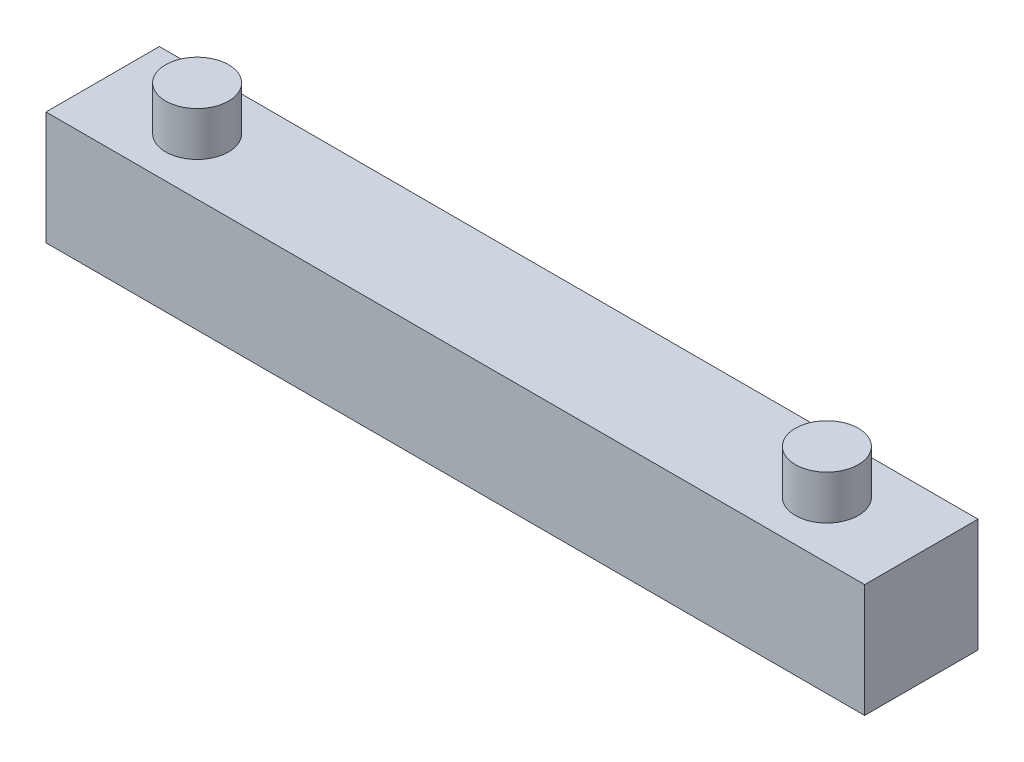
SolidWorks part; units mm, degrees
ref_plane "Front" through (0, 0, 0) normal (0, 0, 1) x (1, 0, 0)
ref_plane "Top" through (0, 0, 0) normal (0, 1, 0) x (1, 0, 0)
ref_plane "Right" through (0, 0, 0) normal (1, 0, 0) x (0, 0, -1)
sketch "Sketch1" plane through (0, 0, 0) normal (0, 1, 0) x (1, 0, 0)
  line L1 (32.5, 4.5) -> (-32.5, 4.5)
  line L2 (32.5, 4.5) -> (32.5, -4.5)
  line L3 (32.5, -4.5) -> (-32.5, -4.5)
  line L4 (-32.5, 4.5) -> (-32.5, -4.5)
  line L5 (32.5, 4.5) -> (-32.5, -4.5) construction
  line L6 (32.5, -4.5) -> (-32.5, 4.5) construction
  point P0 (0, 0)
  dimension "D1" = 65
  dimension "D2" = 9
extrude "Boss-Extrude1" add sketch "Sketch1" along normal blind 9
sketch "Sketch2" plane through (0, 9, 0) normal (0, 1, 0) x (1, 0, 0)
  line L0 (-32.5, 4.5) -> (-32.5, -4.5) construction
  circle A0 centre (-25, 0) radius 2.5
  circle A1 centre (25, 0) radius 2.5
  dimension "D1" = 50
  dimension "D2" = 5
  dimension "D3" = 7.5
extrude "Boss-Extrude2" add sketch "Sketch2" along normal blind 3.5
